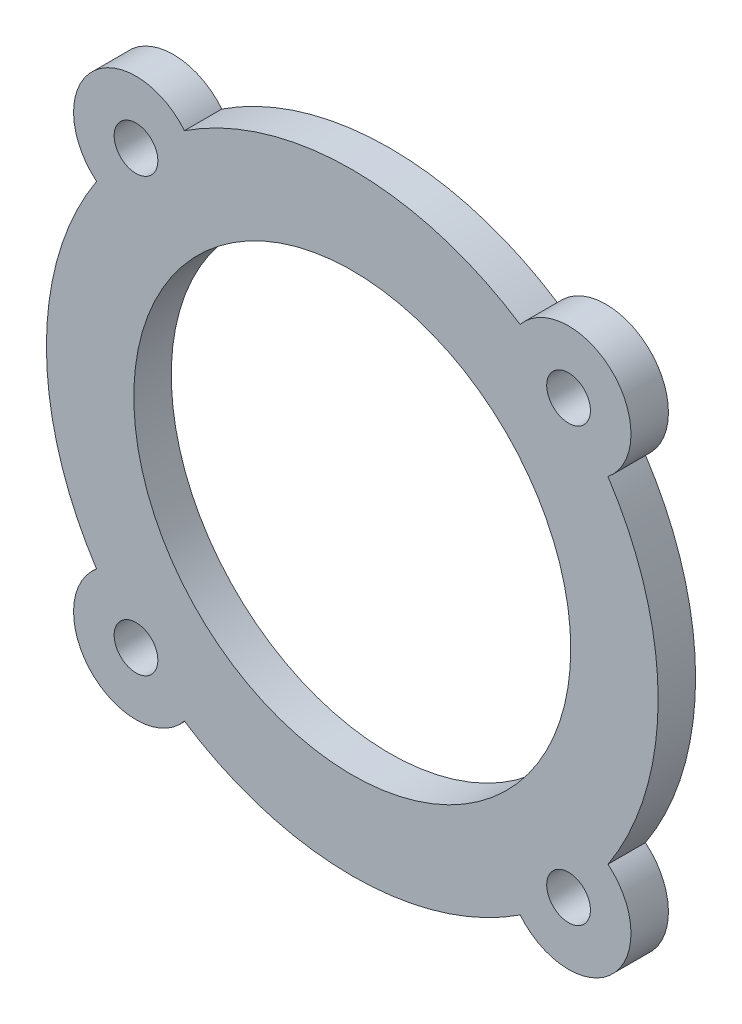
SolidWorks part; units mm, degrees
ref_plane "前视基准面" through (0, 0, 0) normal (0, 0, 1) x (1, 0, 0)
ref_plane "上视基准面" through (0, 0, 0) normal (0, 1, 0) x (1, 0, 0)
ref_plane "右视基准面" through (0, 0, 0) normal (1, 0, 0) x (0, 0, -1)
sketch "草图1" plane through (0, 0, 0) normal (0, 0, 1) x (1, 0, 0)
  line L9 (-17.3241, -17.3241) -> (17.3241, -17.3241) construction
  line L10 (-17.3241, -17.3241) -> (-17.3241, 17.3241) construction
  line L11 (-17.3241, 17.3241) -> (17.3241, 17.3241) construction
  line L12 (17.3241, -17.3241) -> (17.3241, 17.3241) construction
  line L13 (-17.3241, -17.3241) -> (17.3241, 17.3241) construction
  line L14 (-17.3241, 17.3241) -> (17.3241, -17.3241) construction
  circle A0 centre (0, 0) radius 17.5
  circle A15 centre (-17.3241, 17.3241) radius 1.75
  circle A20 centre (17.3241, 17.3241) radius 1.75
  circle A21 centre (17.3241, -17.3241) radius 1.75
  circle A22 centre (-17.3241, -17.3241) radius 1.75
  arc A24 (-13.4463, 20.4804) -> (-20.4804, 13.4463) centre (-17.3241, 17.3241) ccw
  arc A25 (20.4804, 13.4463) -> (13.4463, 20.4804) centre (17.3241, 17.3241) ccw
  arc A26 (13.4463, -20.4804) -> (20.4804, -13.4463) centre (17.3241, -17.3241) ccw
  arc A27 (-20.4804, -13.4463) -> (-13.4463, -20.4804) centre (-17.3241, -17.3241) ccw
  arc A28 (-20.4804, 13.4463) -> (-20.4804, -13.4463) centre (0, 0) ccw
  arc A29 (13.4463, 20.4804) -> (-13.4463, 20.4804) centre (0, 0) ccw
  arc A30 (20.4804, -13.4463) -> (20.4804, 13.4463) centre (0, 0) ccw
  arc A31 (-13.4463, -20.4804) -> (13.4463, -20.4804) centre (0, 0) ccw
  point P17 (0, 0)
  point P25 (0, 0)
  point P28 (0, 0)
  dimension "D1" = 35
  dimension "D2" = 90
  dimension "D3" = 24.5
  dimension "D4" = 3.5
  dimension "D6" = 10
  dimension "D7" = 4
  dimension "D5" = 4
extrude "凸台-拉伸1" add sketch "草图1" along normal blind 3
